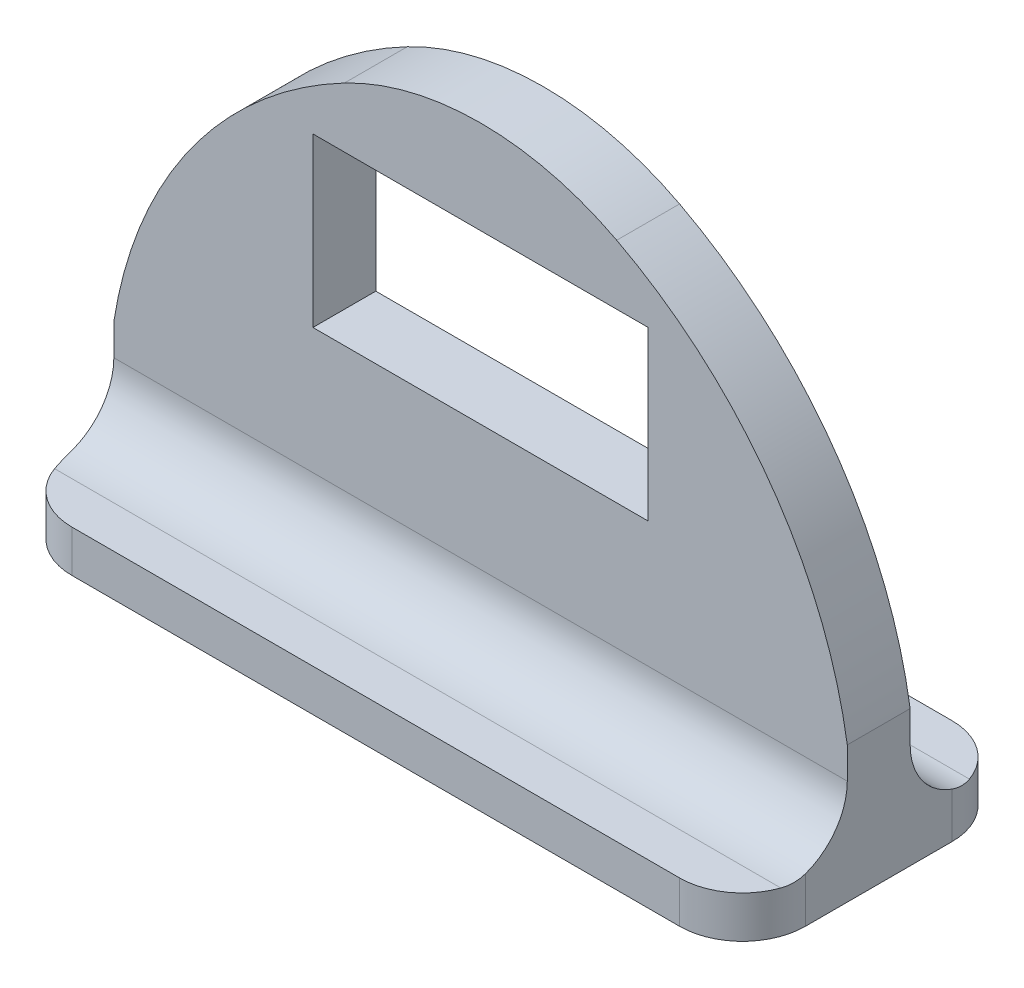
SolidWorks part; units mm, degrees
ref_plane "Front Plane" through (0, 0, 0) normal (0, 0, 1) x (1, 0, 0)
ref_plane "Top Plane" through (0, 0, 0) normal (0, 1, 0) x (1, 0, 0)
ref_plane "Right Plane" through (0, 0, 0) normal (1, 0, 0) x (0, 0, -1)
sketch "Sketch1" plane through (0, 0, 0) normal (0, 0, 1) x (1, 0, 0)
  line L0 (-44.45, 0) -> (44.45, 0)
  line L1 (-20.32, 48.26) -> (20.32, 48.26)
  line L2 (-20.32, 48.26) -> (-20.32, 27.94)
  line L3 (-20.32, 27.94) -> (20.32, 27.94)
  line L4 (20.32, 48.26) -> (20.32, 27.94)
  line L5 (-20.32, 48.26) -> (20.32, 27.94) construction
  line L6 (-20.32, 27.94) -> (20.32, 48.26) construction
  line L7 (-44.45, 0) -> (-44.45, 45.1825)
  line L8 (44.45, 0) -> (44.45, 45.1825)
  arc A0 (-44.45, 0) -> (-16.503, 55.5097) centre (8.255, 8.255) cw
  arc A1 (16.503, 55.5097) -> (44.45, 0) centre (-8.255, 8.255) cw
  arc A2 (198.4097, 119.0742) -> (62.7787, 8.255) centre (44.45, 45.1825) cw
  arc A3 (16.503, 55.5097) -> (-16.503, 55.5097) centre (0, 24.011) ccw
  point P0 (0, 38.1)
  point P9 (0, 0)
  point P18 (0, 60.96)
  dimension "D6" = 35.56
  dimension "D1" = 38.1
  dimension "D2" = 20.32
  dimension "D3" = 40.64
  dimension "D4" = 88.9
  dimension "D5" = 12.7
extrude "Boss-Extrude1" add sketch "Sketch1" along normal blind 7.62 contours A1 A3 A0 L7 L0 L8 L1 L4 L3 L2
sketch "Sketch2" plane through (0, 0, 0) normal (0, 0, -1) x (-1, 0, 0)
  line L0 (44.45, 0) -> (44.45, 16.51) construction
  line L1 (-44.45, 0) -> (44.45, 0)
  line L2 (-44.45, 0) -> (-44.45, 5.08)
  line L3 (-44.45, 5.08) -> (44.45, 5.08)
  line L4 (44.45, 0) -> (44.45, 5.08)
  dimension "D1" = 5.08
sketch "Sketch3" plane through (0, 0, 7.62) normal (0, 0, 1) x (1, 0, 0)
  line L0 (44.45, 0) -> (44.45, 16.51) construction
  line L1 (-44.45, 0) -> (44.45, 0)
  line L2 (-44.45, 0) -> (-44.45, 5.08)
  line L3 (-44.45, 5.08) -> (44.45, 5.08)
  line L4 (44.45, 0) -> (44.45, 5.08)
  dimension "D1" = 5.08
extrude "Boss-Extrude2" add sketch "Sketch2" along normal blind 12.7
extrude "Boss-Extrude3" add sketch "Sketch3" along normal blind 12.7
fillet "Fillet1" radius 7.62 3 edges at (-44.45, 2.54, 20.32) (0, 5.08, 0) (44.45, 2.54, 20.32)
fillet "Fillet2" radius 7.62 3 edges at (-44.45, 2.54, -12.7) (0, 5.08, 7.62) (44.45, 2.54, -12.7)
sketch "Sketch4" plane through (0, 0, 0) normal (0, -1, 0) x (1, 0, 0)
  line L0 (-36.83, 20.32) -> (36.83, 20.32) construction
  circle A0 centre (0, 3.81) radius 15.6335
  point P4 (0, 20.32)
  dimension "D1" = 0
